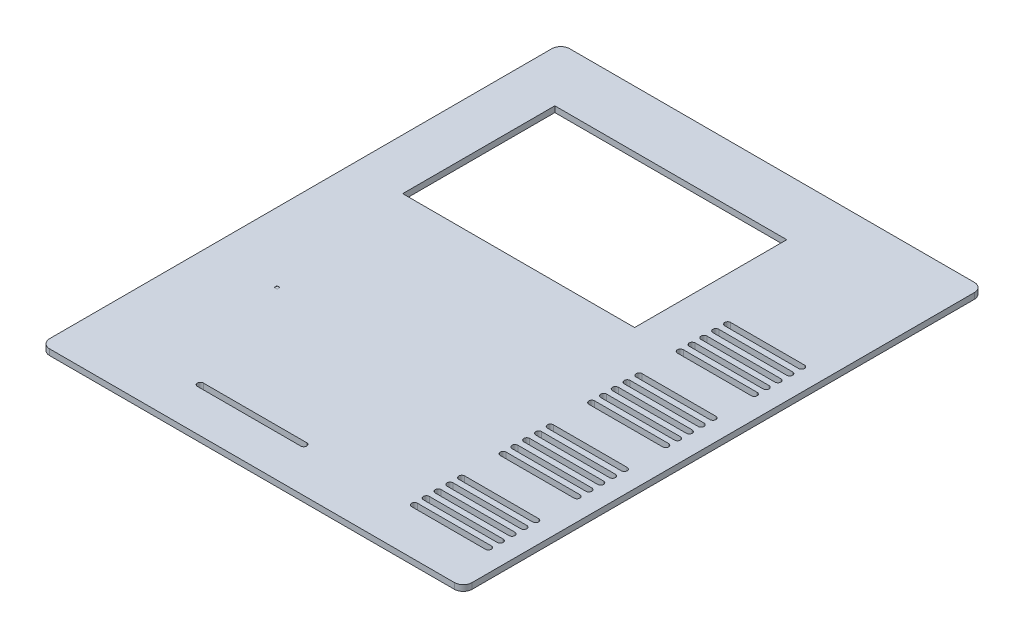
SolidWorks part; units mm, degrees
ref_plane "Front Plane" through (0, 0, 0) normal (0, 0, 1) x (1, 0, 0)
ref_plane "Top Plane" through (0, 0, 0) normal (0, 1, 0) x (1, 0, 0)
ref_plane "Right Plane" through (0, 0, 0) normal (1, 0, 0) x (0, 0, -1)
sketch "Sketch1" plane through (0, 0, 0) normal (0, 1, 0) x (1, 0, 0)
  line L0 (0, -186.2132) -> (0, 178.0816) construction
  line L5 (-46.5, 65.75) -> (-46.5, 14.25) construction
  line L7 (-271.0526, 0) -> (330.1421, 0) construction
  line L9 (-85.75, 65.75) -> (-7.25, 65.75)
  line L10 (-85.75, 65.75) -> (-85.75, 14.25)
  line L11 (-85.75, 14.25) -> (-7.25, 14.25)
  line L12 (-7.25, 65.75) -> (-7.25, 14.25)
  line L15 (-85.75, 40) -> (-7.25, 40) construction
  line L16 (20, -105.7105) -> (20, 127.5903) construction
  line L17 (-90.5, 7.5) -> (-2.5, 7.5) construction
  line L18 (-90.5, 7.5) -> (-90.5, 72.5) construction
  line L19 (-90.5, 72.5) -> (-2.5, 72.5) construction
  line L20 (-2.5, 7.5) -> (-2.5, 72.5) construction
  line L21 (-90.5, 7.5) -> (-2.5, 72.5) construction
  line L22 (-90.5, 72.5) -> (-2.5, 7.5) construction
  line L23 (-93, 5) -> (0, 5) construction
  line L24 (-93, 5) -> (-93, 75) construction
  line L25 (-93, 75) -> (0, 75) construction
  line L26 (0, 5) -> (0, 75) construction
  line L27 (-93, 5) -> (0, 75) construction
  line L28 (-93, 75) -> (0, 5) construction
  line L29 (-81, -81) -> (-12, -81) construction
  line L30 (-81, -81) -> (-81, -5) construction
  line L31 (-81, -5) -> (-12, -5) construction
  line L32 (-12, -81) -> (-12, -5) construction
  line L33 (-81, -81) -> (-12, -5) construction
  line L34 (-81, -5) -> (-12, -81) construction
  line L35 (-64, -77) -> (-29, -77)
  line L36 (-64, -77) -> (-64, -75) construction
  line L37 (-64, -75) -> (-29, -75)
  line L38 (-29, -77) -> (-29, -75) construction
  line L39 (-64, -77) -> (-29, -75) construction
  line L40 (-64, -75) -> (-29, -77) construction
  line L41 (-103, 85) -> (40, 85)
  line L42 (-103, 85) -> (-103, -91)
  line L43 (-103, -91) -> (40, -91)
  line L44 (40, 85) -> (40, -91)
  line L45 (7.5, -70) -> (32.5, -70)
  line L46 (7.5, -76) -> (32.5, -76)
  line L47 (7.5, -76) -> (7.5, -74) construction
  line L48 (7.5, -74) -> (32.5, -74)
  line L49 (32.5, -76) -> (32.5, -74) construction
  line L50 (7.5, -76) -> (32.5, -74) construction
  line L51 (7.5, -74) -> (32.5, -76) construction
  line L52 (7.5, -72) -> (32.5, -72)
  line L53 (7.5, -66) -> (32.5, -66)
  line L54 (7.5, -68) -> (32.5, -68)
  line L55 (7.5, -62) -> (32.5, -62)
  line L56 (7.5, -64) -> (32.5, -64)
  line L57 (7.5, -58) -> (32.5, -58)
  line L58 (7.5, -60) -> (32.5, -60)
  line L59 (7.5, -40) -> (32.5, -40)
  line L60 (7.5, -46) -> (32.5, -46)
  line L61 (7.5, -44) -> (32.5, -44)
  line L62 (7.5, -42) -> (32.5, -42)
  line L63 (7.5, -36) -> (32.5, -36)
  line L64 (7.5, -38) -> (32.5, -38)
  line L65 (7.5, -32) -> (32.5, -32)
  line L66 (7.5, -34) -> (32.5, -34)
  line L67 (7.5, -28) -> (32.5, -28)
  line L68 (7.5, -30) -> (32.5, -30)
  line L69 (7.5, -46) -> (7.5, -44) construction
  line L70 (32.5, -46) -> (32.5, -44) construction
  line L71 (7.5, -46) -> (32.5, -44) construction
  line L72 (7.5, -44) -> (32.5, -46) construction
  line L73 (7.5, -10) -> (32.5, -10)
  line L74 (7.5, -16) -> (32.5, -16)
  line L75 (7.5, -14) -> (32.5, -14)
  line L76 (7.5, -12) -> (32.5, -12)
  line L77 (7.5, -6) -> (32.5, -6)
  line L78 (7.5, -8) -> (32.5, -8)
  line L79 (7.5, -2) -> (32.5, -2)
  line L80 (7.5, -4) -> (32.5, -4)
  line L81 (7.5, 2) -> (32.5, 2)
  line L82 (7.5, 0) -> (32.5, 0)
  line L83 (7.5, -16) -> (7.5, -14) construction
  line L84 (32.5, -16) -> (32.5, -14) construction
  line L85 (7.5, -16) -> (32.5, -14) construction
  line L86 (7.5, -14) -> (32.5, -16) construction
  line L87 (7.5, 20) -> (32.5, 20)
  line L88 (7.5, 14) -> (32.5, 14)
  line L89 (7.5, 16) -> (32.5, 16)
  line L90 (7.5, 18) -> (32.5, 18)
  line L91 (7.5, 24) -> (32.5, 24)
  line L92 (7.5, 22) -> (32.5, 22)
  line L93 (7.5, 28) -> (32.5, 28)
  line L94 (7.5, 26) -> (32.5, 26)
  line L95 (7.5, 32) -> (32.5, 32)
  line L96 (7.5, 30) -> (32.5, 30)
  line L97 (7.5, 14) -> (7.5, 16) construction
  line L98 (32.5, 14) -> (32.5, 16) construction
  line L99 (7.5, 14) -> (32.5, 16) construction
  line L100 (7.5, 16) -> (32.5, 14) construction
  circle A0 centre (-90.5, 7.5) radius 1.75 construction
  circle A1 centre (-2.5, 7.5) radius 1.75 construction
  circle A2 centre (-2.5, 72.5) radius 1.75 construction
  circle A3 centre (-90.5, 72.5) radius 1.75 construction
  arc A4 (-64, -77) -> (-64, -75) centre (-64, -76) cw
  arc A5 (-29, -75) -> (-29, -77) centre (-29, -76) cw
  arc A6 (7.5, -74) -> (7.5, -76) centre (7.5, -75) ccw
  arc A7 (32.5, -74) -> (32.5, -76) centre (32.5, -75) cw
  arc A8 (7.5, -70) -> (7.5, -72) centre (7.5, -71) ccw
  arc A9 (32.5, -70) -> (32.5, -72) centre (32.5, -71) cw
  arc A10 (7.5, -66) -> (7.5, -68) centre (7.5, -67) ccw
  arc A11 (32.5, -66) -> (32.5, -68) centre (32.5, -67) cw
  arc A12 (7.5, -62) -> (7.5, -64) centre (7.5, -63) ccw
  arc A13 (32.5, -62) -> (32.5, -64) centre (32.5, -63) cw
  arc A14 (7.5, -58) -> (7.5, -60) centre (7.5, -59) ccw
  arc A15 (32.5, -58) -> (32.5, -60) centre (32.5, -59) cw
  arc A16 (7.5, -44) -> (7.5, -46) centre (7.5, -45) ccw
  arc A17 (32.5, -44) -> (32.5, -46) centre (32.5, -45) cw
  arc A18 (7.5, -40) -> (7.5, -42) centre (7.5, -41) ccw
  arc A19 (32.5, -40) -> (32.5, -42) centre (32.5, -41) cw
  arc A20 (7.5, -36) -> (7.5, -38) centre (7.5, -37) ccw
  arc A21 (32.5, -36) -> (32.5, -38) centre (32.5, -37) cw
  arc A22 (7.5, -32) -> (7.5, -34) centre (7.5, -33) ccw
  arc A23 (32.5, -32) -> (32.5, -34) centre (32.5, -33) cw
  arc A24 (7.5, -28) -> (7.5, -30) centre (7.5, -29) ccw
  arc A25 (32.5, -28) -> (32.5, -30) centre (32.5, -29) cw
  arc A26 (7.5, -14) -> (7.5, -16) centre (7.5, -15) ccw
  arc A27 (32.5, -14) -> (32.5, -16) centre (32.5, -15) cw
  arc A28 (7.5, -10) -> (7.5, -12) centre (7.5, -11) ccw
  arc A29 (32.5, -10) -> (32.5, -12) centre (32.5, -11) cw
  arc A30 (7.5, -6) -> (7.5, -8) centre (7.5, -7) ccw
  arc A31 (32.5, -6) -> (32.5, -8) centre (32.5, -7) cw
  arc A32 (7.5, -2) -> (7.5, -4) centre (7.5, -3) ccw
  arc A33 (32.5, -2) -> (32.5, -4) centre (32.5, -3) cw
  arc A34 (7.5, 2) -> (7.5, 0) centre (7.5, 1) ccw
  arc A35 (32.5, 2) -> (32.5, 0) centre (32.5, 1) cw
  arc A36 (7.5, 16) -> (7.5, 14) centre (7.5, 15) ccw
  arc A37 (32.5, 16) -> (32.5, 14) centre (32.5, 15) cw
  arc A38 (7.5, 20) -> (7.5, 18) centre (7.5, 19) ccw
  arc A39 (32.5, 20) -> (32.5, 18) centre (32.5, 19) cw
  arc A40 (7.5, 24) -> (7.5, 22) centre (7.5, 23) ccw
  arc A41 (32.5, 24) -> (32.5, 22) centre (32.5, 23) cw
  arc A42 (7.5, 28) -> (7.5, 26) centre (7.5, 27) ccw
  arc A43 (32.5, 28) -> (32.5, 26) centre (32.5, 27) cw
  arc A44 (7.5, 32) -> (7.5, 30) centre (7.5, 31) ccw
  arc A45 (32.5, 32) -> (32.5, 30) centre (32.5, 31) cw
  point P0 (0, 0)
  point P1 (-46.5, 40)
  point P18 (-46.5, 40)
  point P25 (-46.5, 40)
  point P29 (-46.5, -43)
  point P35 (-46.5, -76)
  point P47 (20, -75)
  point P80 (20, -45)
  point P111 (20, -15)
  point P142 (20, 15)
  dimension "D7" = 3.5
  dimension "D1" = 51.5
  dimension "D2" = 78.5
  dimension "D3" = 65
  dimension "D4" = 88
  dimension "D5" = 70
  dimension "D6" = 93
  dimension "D8" = 20
  dimension "D9" = 5
  dimension "D10" = 69
  dimension "D11" = 76
  dimension "D12" = 10
  dimension "D13" = 2
  dimension "D14" = 35
  dimension "D15" = 4
  dimension "D16" = 10
  dimension "D17" = 10
  dimension "D18" = 10
  dimension "D19" = 40
  dimension "D20" = 25
  dimension "D21" = 2
  dimension "D22" = 15
  dimension "D23" = 5
  dimension "D24" = 4
extrude "Boss-Extrude1" add sketch "Sketch1" along normal blind 2
sketch "Sketch2" plane through (0, 2, 0) normal (0, 1, 0) x (1, 0, 0)
  line L0 (-103, 85) -> (-103, -91) construction
  line L1 (-80, -34) -> (-79, -34)
  line L2 (-80, -34) -> (-80, -35)
  line L3 (-80, -35) -> (-79, -35)
  line L4 (-79, -34) -> (-79, -35)
  line L5 (-29, -75) -> (-64, -75) construction
  dimension "D1" = 1
  dimension "D2" = 1
  dimension "D3" = 23
  dimension "D4" = 40
extrude "Cut-Extrude1" cut sketch "Sketch2" against normal blind 0.1 contours L2 L1 L4 L3
fillet "Fillet1" radius 3 4 edges at (-103, 1, -85) (40, 1, -85) (40, 1, 91) (-103, 1, 91)
